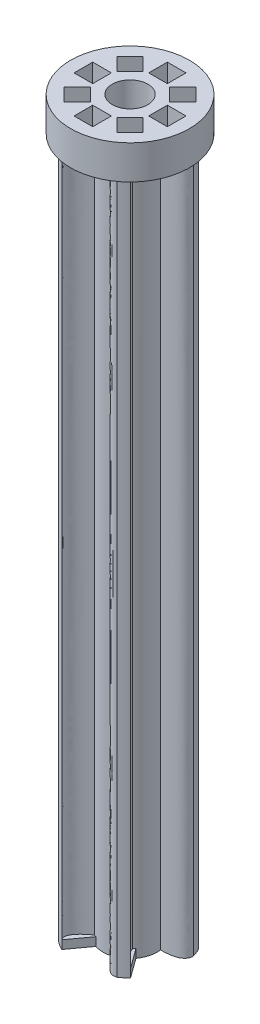
SolidWorks part; units mm, degrees
material "ABS PC"
ref_plane "Front Plane" through (0, 0, 0) normal (0, 0, 1) x (1, 0, 0)
ref_plane "Top Plane" through (0, 0, 0) normal (0, 1, 0) x (1, 0, 0)
ref_plane "Right Plane" through (0, 0, 0) normal (1, 0, 0) x (0, 0, -1)
sketch "Sketch1" plane through (0, 0, 0) normal (0, 1, 0) x (1, 0, 0)
  circle A0 centre (0, 0) radius 1.6
  circle A3 centre (0, 0) radius 1.1
  dimension "D1" = 3.2
extrude "Boss-Extrude1" add sketch "Sketch1" along normal blind 41
sketch "Sketch2" plane through (0, 41, 0) normal (0, 1, 0) x (1, 0, 0)
  circle A0 centre (0, 0) radius 3
  circle A2 centre (0, 0) radius 1.05
extrude "Boss-Extrude2" add sketch "Sketch2" along normal blind 2
sketch "Sketch4" plane through (0, 43, 0) normal (0, 1, 0) x (1, 0, 0)
  line L0 (0, 0) -> (0, 2.2) construction
  line L2 (-0.55, 2.75) -> (0.55, 2.75)
  line L3 (-0.55, 2.75) -> (-0.55, 1.65)
  line L4 (-0.55, 1.65) -> (0.55, 1.65)
  line L5 (0.55, 2.75) -> (0.55, 1.65)
  line L6 (0, 1.65) -> (0, 2.75) construction
  line L7 (-0.55, 2.2) -> (0.55, 2.2) construction
  dimension "D1" = 1.1
  dimension "D2" = 1.1
extrude "Cut-Extrude2" cut sketch "Sketch4" against normal blind 1.5
pattern_circular "CirPattern2" count 8 over 360 about axis through (0, 0, 0) along (0, 1, 0) of "Cut-Extrude2"
sketch "Sketch6" plane through (0, 41, 0) normal (0, -1, 0) x (1, 0, 0)
  line L0 (1.5865, -0.2076) -> (2.8745, -0.2076) construction
  line L1 (2.8745, -0.2076) -> (2.8745, -0.8586) construction
  line L2 (1.3743, -0.8194) -> (2.6636, -0.8293) construction
  line L3 (2.6636, -0.8293) -> (2.6636, -1.3803) construction
  line L5 (1.5865, -0.2076) -> (2.8745, -0.2076) construction
  arc A2 (1.5865, -0.2076) -> (1.3743, -0.8194) centre (0, 0) cw
  circle A3 centre (0, 0) radius 1.6 construction
  circle A13 centre (0, 0) radius 3 construction
  arc A14 (2.8745, -0.8586) -> (2.6636, -1.3803) centre (0, 0) cw
  spline S0 degree 2 poles (1.5865, -0.2076) (2.8745, -0.2076) (2.8745, -0.8586) knots 0 0 0 1 1 1
  spline S1 degree 2 poles (1.3743, -0.8194) (2.6636, -0.8293) (2.6636, -1.3803) knots 0 0 0 1 1 1
extrude "Boss-Extrude3" add sketch "Sketch6" along normal blind 41
sketch "Sketch7" plane through (0, 0, 0) normal (0, 1, 0) x (1, 0, 0)
  line L0 (1.2976, 0.936) -> (2.6636, 1.3803)
  line L1 (1.3743, 0.8194) -> (2.8745, 0.8586) construction
  line L2 (2.8745, 0.8586) -> (2.6636, 1.3803) construction
  arc A3 (1.3743, 0.8194) -> (1.2976, 0.936) centre (0, 0) ccw
  spline S0 degree 2 poles (1.3743, 0.8194) (2.8745, 0.8586) (2.6636, 1.3803) knots 0 0 0 1 1 1
extrude "Boss-Extrude4" add sketch "Sketch7" along normal blind 0.5
pattern_circular "CirPattern3" count 5 over 360 about axis through (0, 41, 0) along (0, -1, 0) of "Boss-Extrude3", "Boss-Extrude4"
sketch "Sketch9" plane through (0, 41, 0) normal (0, -1, 0) x (1, 0, 0)
  circle A0 centre (0, 0) radius 3.5
  circle A1 centre (0, 0) radius 3
  dimension "D1" = 0.5
extrude "Boss-Extrude5" add sketch "Sketch9" against normal blind 2
